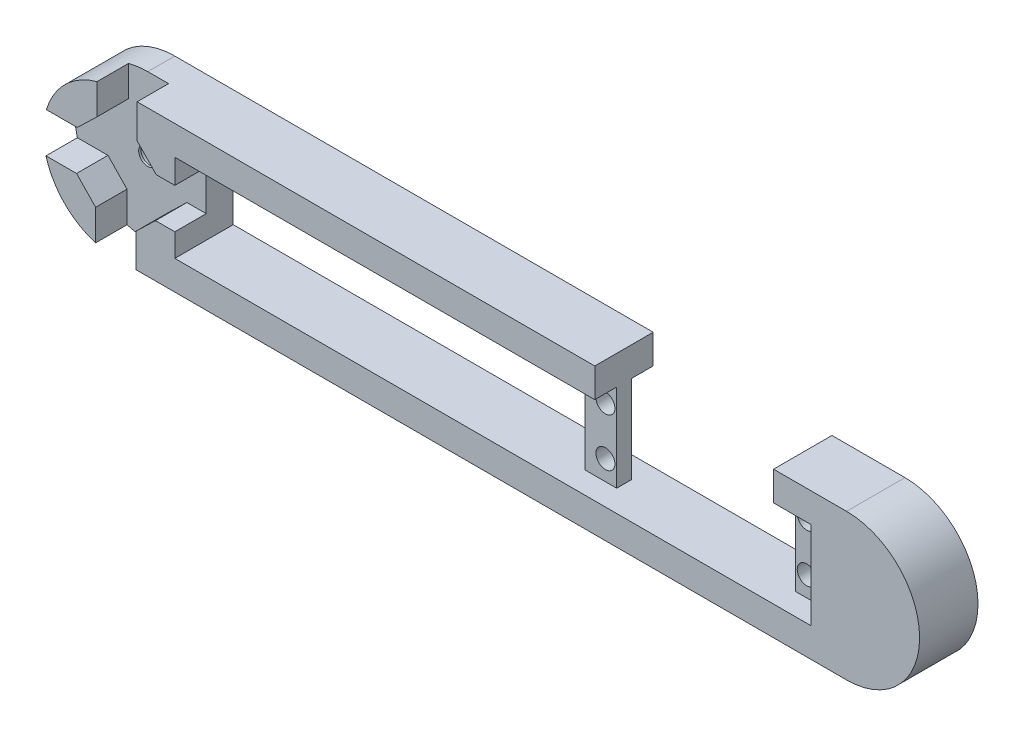
SolidWorks part; units mm, degrees
ref_plane "Plan de face" through (0, 0, 0) normal (0, 0, 1) x (1, 0, 0)
ref_plane "Plan de dessus" through (0, 0, 0) normal (0, 1, 0) x (1, 0, 0)
ref_plane "Plan de droite" through (0, 0, 0) normal (1, 0, 0) x (0, 0, -1)
sketch "Esquisse1" plane through (0, 0, 0) normal (0, 0, 1) x (1, 0, 0)
  line L0 (50, -10.9971) -> (50, 26.1419) construction
  line L1 (0, 0) -> (100, 0)
  line L3 (0, 20) -> (100, 20)
  arc A0 (0, 0) -> (0, 20) centre (0, 10) cw
  arc A1 (100, 0) -> (100, 20) centre (100, 10) ccw
  point P9 (50, 0)
  point P11 (50, 20)
  dimension "D3" = 10
  dimension "D1" = 20
  dimension "D2" = 50
extrude "Boss.-Extru.1" add sketch "Esquisse1" along normal blind 8
sketch "Esquisse4" plane through (0, 0, 8) normal (0, 0, 1) x (1, 0, 0)
  line L0 (100, 20) -> (0, 20) construction
  line L1 (8, 4) -> (90, 4)
  line L2 (8, 4) -> (8, 16)
  line L3 (8, 16) -> (90, 16)
  line L4 (90, 4) -> (90, 16)
  line L5 (0, 0) -> (100, 0) construction
  dimension "D1" = 4
  dimension "D2" = 4
  dimension "D4" = 82
extrude "Enlèv. mat.-Extru.3" cut sketch "Esquisse4" against normal through all
sketch "Esquisse6" plane through (0, 4, 0) normal (0, 1, 0) x (1, 0, 0)
  line L0 (8, 0) -> (90, 0) construction
  line L1 (65.5152, 0) -> (61.1972, 0)
  line L2 (65.5152, 0) -> (65.5152, -8)
  line L3 (65.5152, -8) -> (61.1972, -8)
  line L4 (61.1972, 0) -> (61.1972, -8)
  line L5 (8, -8) -> (90, -8) construction
  line L6 (66.0152, -3) -> (66.0152, -19.891) construction
  dimension "D1" = 0.5
extrude "Boss.-Extru.2" add sketch "Esquisse6" along normal up to next
sketch "Esquisse7" plane through (0, 0, 0) normal (0, 0, -1) x (-1, 0, 0)
  line L1 (-77.7576, 1.4503) -> (-77.7576, 23.5897) construction
  line L2 (-90, 4) -> (-90, 16) construction
  line L3 (-65.5152, 16) -> (-65.5152, 4) construction
  circle A0 centre (-91.5422, 13.344) radius 1.3
  circle A2 centre (-91.5422, 6.74) radius 1.3
  circle A3 centre (-63.973, 6.74) radius 1.3
  circle A5 centre (-63.973, 13.344) radius 1.3
  dimension "D1" = 2.6
extrude "Enlèv. mat.-Extru.5" cut sketch "Esquisse7" against normal blind 10
sketch "Esquisse8" plane through (0, 0, 8) normal (0, 0, 1) x (1, 0, 0)
  line L1 (95.0986, 16) -> (90, 16)
  line L2 (95.0986, 16) -> (95.0986, 4)
  line L3 (95.0986, 4) -> (90, 4)
  line L4 (90, 16) -> (90, 4)
  line L5 (65.5152, 16) -> (61.1972, 16)
  line L6 (65.5152, 16) -> (65.5152, 4)
  line L7 (65.5152, 4) -> (61.1972, 4)
  line L8 (61.1972, 16) -> (61.1972, 4)
  line L9 (65.5152, 16) -> (65.5152, 4) construction
  line L10 (90, 16) -> (65.5152, 16) construction
  line L11 (8, 4) -> (61.1972, 4) construction
  line L12 (61.1972, 16) -> (61.1972, 4) construction
extrude "Enlèv. mat.-Extru.6" cut sketch "Esquisse8" against normal blind 3
sketch "Esquisse13" plane through (0, 0, 8) normal (0, 0, 1) x (1, 0, 0)
  circle A0 centre (0, 10) radius 4
  arc A1 (0, 20) -> (0, 0) centre (0, 10) ccw construction
  dimension "D1" = 8
extrude "Enlèv. mat.-Extru.9" cut sketch "Esquisse13" against normal blind 4.3
sketch "Esquisse14" plane through (0, 0, 8) normal (0, 0, 1) x (1, 0, 0)
  line L0 (2.6554, 4.5441) -> (2.6554, -2.0086)
  line L1 (-2.6554, 22.0086) -> (2.8446, 21.9124)
  line L2 (-2.8446, -1.9124) -> (-2.8446, 4.6403)
  line L4 (12.0086, 12.6554) -> (11.9124, 7.1554)
  line L7 (2.6554, -2.0086) -> (-2.8446, -1.9124)
  line L10 (-12.0086, 7.3446) -> (-11.9124, 12.8446)
  line L12 (5.4559, 12.6554) -> (2.8446, 15.3597)
  line L13 (2.6554, 4.5441) -> (5.3597, 7.1554)
  line L14 (-2.6554, 15.4559) -> (-5.3597, 12.8446)
  line L15 (-5.4559, 7.3446) -> (-2.8446, 4.6403)
  line L16 (5.3597, 7.1554) -> (11.9124, 7.1554)
  line L17 (5.4559, 12.6554) -> (12.0086, 12.6554)
  line L18 (2.8446, 15.3597) -> (2.8446, 21.9124)
  line L19 (-2.6554, 15.4559) -> (-2.6554, 22.0086)
  line L20 (-5.3597, 12.8446) -> (-11.9124, 12.8446)
  line L21 (-5.4559, 7.3446) -> (-12.0086, 7.3446)
  circle A3 centre (0, 10) radius 6.0678 construction
  dimension "D1" = 5.5
  dimension "D2" = 6.5527
extrude "Enlèv. mat.-Extru.10" cut sketch "Esquisse14" against normal blind 4.3
sketch "Esquisse15" plane through (0, 0, 0) normal (0, 0, -1) x (-1, 0, 0)
  circle A0 centre (0, 10) radius 2.5
  arc A1 (0, 0) -> (0, 20) centre (0, 10) ccw construction
  dimension "D1" = 5
extrude "Enlèv. mat.-Extru.11" cut sketch "Esquisse15" against normal blind 3.4
sketch "Esquisse16" plane through (0, 0, 3.4) normal (0, 0, -1) x (-1, 0, 0)
  circle A0 centre (0, 10) radius 1.25
  circle A1 centre (0, 10) radius 2.5 construction
  dimension "D1" = 2.5
extrude "Enlèv. mat.-Extru.12" cut sketch "Esquisse16" against normal up to next
sketch "Esquisse17" plane through (0, 20, 0) normal (0, 1, 0) x (1, 0, 0)
  line L0 (100, -8) -> (2.8446, -8) construction
  line L1 (90, -8) -> (65.5152, -8)
  line L2 (90, -8) -> (90, 0)
  line L3 (90, 0) -> (65.5152, 0)
  line L4 (65.5152, -8) -> (65.5152, 0)
  line L5 (100, 0) -> (0, 0) construction
  line L6 (90, 0) -> (90, -5) construction
  line L7 (65.5152, -5) -> (65.5152, 0) construction
extrude "Enlèv. mat.-Extru.13" cut sketch "Esquisse17" against normal blind 4.3
sketch "Esquisse18" plane through (0, 0, 0) normal (0, 0, -1) x (-1, 0, 0)
  line L0 (-77.7576, 33.2611) -> (-77.7576, -5.5666) construction
  line L1 (-65.5152, 4) -> (-61.1972, 4)
  line L2 (-65.5152, 4) -> (-65.5152, 16)
  line L3 (-65.5152, 16) -> (-61.1972, 16)
  line L4 (-61.1972, 4) -> (-61.1972, 16)
  line L5 (-65.5152, 20) -> (-65.5152, 4) construction
  line L6 (-90, 4) -> (-90, 20) construction
  line L7 (-90, 4) -> (-94.318, 4)
  line L8 (-90, 4) -> (-90, 16)
  line L9 (-90, 16) -> (-94.318, 16)
  line L10 (-94.318, 4) -> (-94.318, 16)
extrude "Enlèv. mat.-Extru.14" cut sketch "Esquisse18" against normal blind 3
